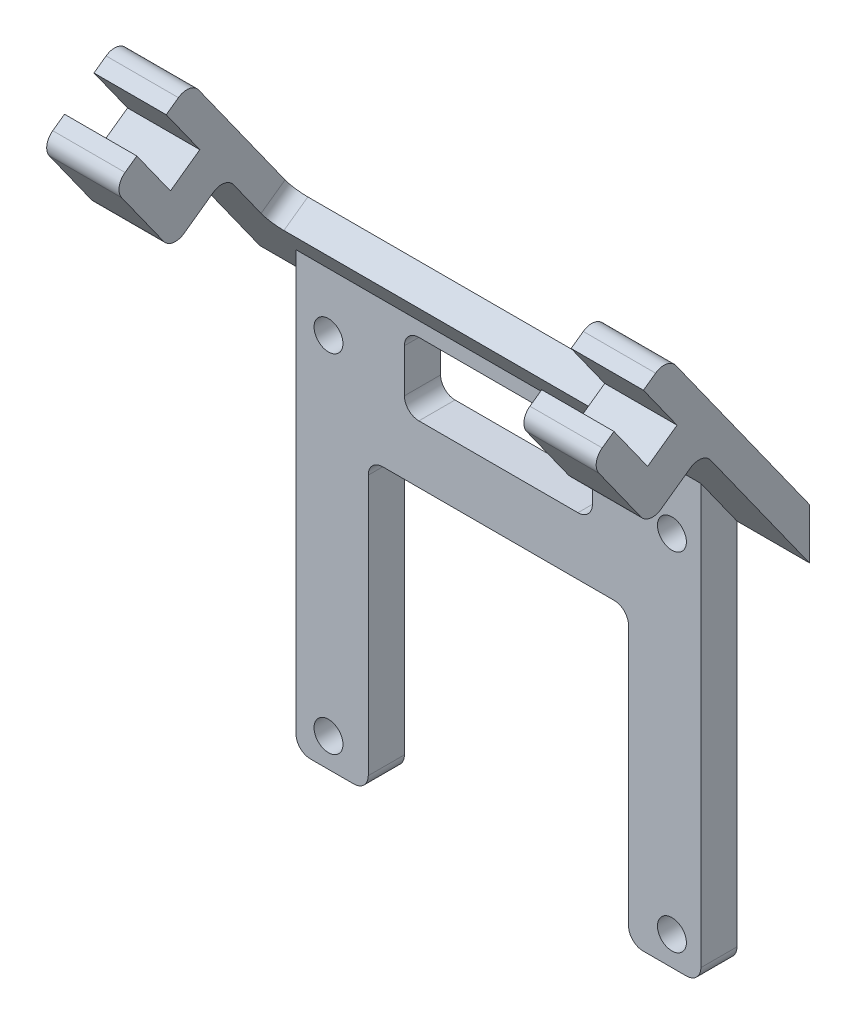
SolidWorks part; units mm, degrees
ref_plane "Alzado" through (0, 0, 0) normal (0, 0, 1) x (1, 0, 0)
ref_plane "Planta" through (0, 0, 0) normal (0, 1, 0) x (1, 0, 0)
ref_plane "Vista lateral" through (0, 0, 0) normal (1, 0, 0) x (0, 0, -1)
sketch "Croquis1" plane through (0, 0, 0) normal (0, 0, 1) x (1, 0, 0)
  line L0 (-9, -15) -> (-14, -15)
  line L1 (14, 15) -> (-14, 15)
  line L2 (14, 15) -> (14, -15)
  line L3 (14, -15) -> (9, -15)
  line L4 (-14, 15) -> (-14, -15)
  line L5 (-9, 5) -> (-9, -15)
  line L6 (9, 5) -> (9, -15)
  line L7 (-9, 5) -> (9, 5)
extrude "Saliente-Extruir1" add sketch "Croquis1" along normal blind 2.5
sketch "Croquis6" plane through (0, 0, 0) normal (1, 0, 0) x (0, 0, -1)
  line L0 (0, 14.9981) -> (0, 11.4973)
  line L1 (0, 14.9981) -> (-11.5586, 31.1942)
  line L2 (0, 11.4973) -> (-11.5586, 27.6934)
  line L3 (-11.5586, 31.1942) -> (-11.5586, 27.6934)
extrude "Saliente-Extruir2" add sketch "Croquis6" along normal blind 19 and the other way blind 19
sketch "Croquis3" plane through (0, 0, 2.5) normal (0, 0, 1) x (1, 0, 0)
  circle A0 centre (-11.75, -13) radius 1
  circle A1 centre (-11.75, 11) radius 1
  circle A2 centre (12, -13) radius 1
  circle A3 centre (12, 11) radius 1
extrude "Cortar-Extruir2" cut sketch "Croquis3" against normal blind 2.5
sketch "Croquis2" plane through (0, 0, 2.5) normal (0, 0, 1) x (1, 0, 0)
  line L1 (-6.5, 14) -> (6.5, 14)
  line L2 (-6.5, 14) -> (-6.5, 9)
  line L3 (-6.5, 9) -> (6.5, 9)
  line L4 (6.5, 14) -> (6.5, 9)
extrude "Cortar-Extruir1" cut sketch "Croquis2" against normal blind 3
fillet "Redondeo1" radius 1 10 edges at (14, -15, 1.25) (9, -15, 1.25) (-9, -15, 1.25) (-14, -15, 1.25) (9, 5, 1.25) (-9, 5, 1.25) (6.5, 14, 1.25) (6.5, 9, 1.25) (-6.5, 9, 1.25) (-6.5, 14, 1.25)
sketch "Croquis7" plane through (0, 5.0611, -7.0917) normal (0, 0.5809, -0.814) x (-1, 0, 0)
  line L0 (19, 32.1057) -> (-19, 32.1057) construction
  line L1 (-14, 32.1057) -> (14, 32.1057)
  line L2 (-14, 32.1057) -> (-14, 16.8182)
  line L3 (-14, 16.8182) -> (14, 16.8182)
  line L4 (14, 32.1057) -> (14, 16.8182)
extrude "Cortar-Extruir3" cut sketch "Croquis7" against normal blind 2.5
sketch "Croquis8" plane through (0, 5.0611, -7.0917) normal (0, 0.5809, -0.814) x (-1, 0, 0)
  line L0 (-19, 12.208) -> (-19, 32.1057) construction
  line L1 (-14, 32.1057) -> (-19, 32.1057)
  line L2 (-14, 32.1057) -> (-14, 29.1057)
  line L3 (-14, 29.1057) -> (-19, 29.1057)
  line L4 (-19, 32.1057) -> (-19, 29.1057)
  dimension "D1" = 3
extrude "Cortar-Extruir4" cut sketch "Croquis8" against normal blind 2.5
mirror "Simetría1" about plane through (0, 0, 0) normal (1, 0, 0) of "Cortar-Extruir4"
fillet "Redondeo2" radius 1 2 edges at (-16.5, 28.7523, 9.8159) (16.5, 28.7523, 9.8159)
sketch "Croquis9" plane through (0, 3.8798, -5.4364) normal (0, -0.5809, 0.814) x (1, 0, 0)
  line L0 (-14, 29.1057) -> (-14, 16.8182) construction
  line L1 (-14, 25.1057) -> (-19, 25.1057)
  line L2 (-14, 25.1057) -> (-14, 22.1057)
  line L3 (-14, 22.1057) -> (-19, 22.1057)
  line L4 (-19, 25.1057) -> (-19, 22.1057)
  line L5 (-19, 29.1057) -> (-19, 9.3585) construction
extrude "Saliente-Extruir3" add sketch "Croquis9" along normal blind 4.5
sketch "Croquis10" plane through (0, 20.4353, 14.584) normal (0, 0.814, 0.5809) x (1, 0, 0)
  line L0 (-19, 2.1788) -> (-19, 6.6788) construction
  line L1 (-14, 2.1788) -> (-19, 2.1788)
  line L2 (-14, 2.1788) -> (-14, 4.1788)
  line L3 (-14, 4.1788) -> (-19, 4.1788)
  line L4 (-19, 2.1788) -> (-19, 4.1788)
extrude "Saliente-Extruir4" add sketch "Croquis10" along normal blind 4
fillet "Redondeo3" radius 1 3 edges at (-16.5, 24.9569, 15.1341) (-16.5, 19.2591, 11.0678) (-16.5, 21.8731, 7.4049)
mirror "Simetría3" about plane through (0, 0, 0) normal (1, 0, 0) of "Redondeo3", "Saliente-Extruir4", "Saliente-Extruir3"
fillet "Redondeo4" radius 1 2 edges at (14, 18.16, 3.5058) (-14, 18.16, 3.5058)
